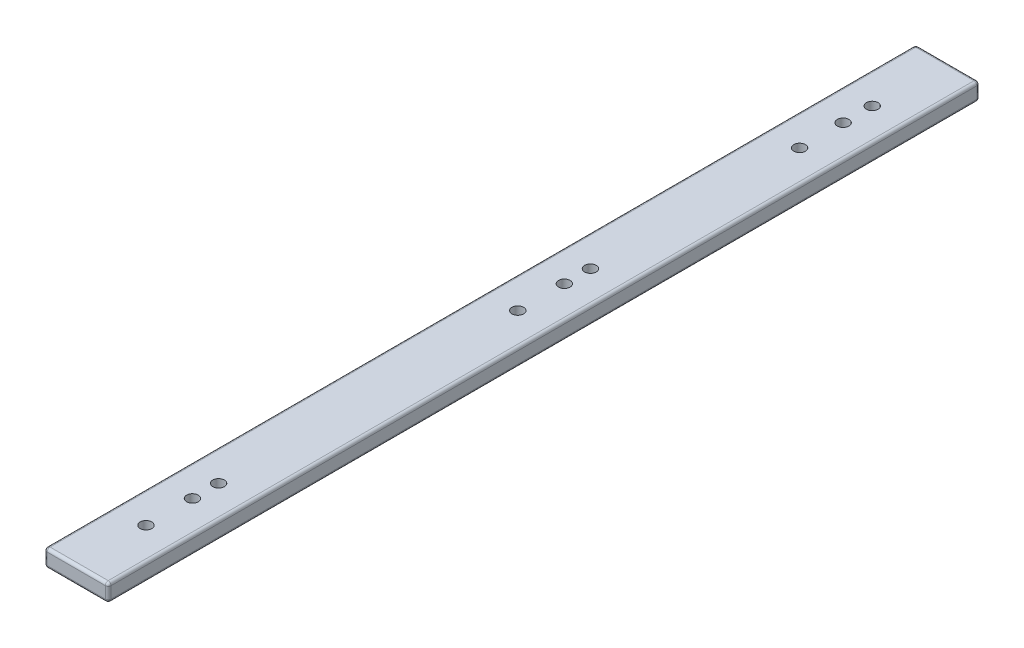
SolidWorks part; units mm, degrees
ref_plane "Front Plane" through (0, 0, 0) normal (0, 0, 1) x (1, 0, 0)
ref_plane "Top Plane" through (0, 0, 0) normal (0, 1, 0) x (1, 0, 0)
ref_plane "Right Plane" through (0, 0, 0) normal (1, 0, 0) x (0, 0, -1)
sketch "Sketch1" plane through (0, 0, 0) normal (0, 0, 1) x (1, 0, 0)
  line L1 (-11, -3) -> (11, -3)
  line L2 (-11, -3) -> (-11, 3)
  line L3 (-11, 3) -> (11, 3)
  line L4 (11, -3) -> (11, 3)
  line L5 (-11, -3) -> (11, 3) construction
  line L6 (-11, 3) -> (11, -3) construction
  point P0 (0, 0)
  dimension "D1" = 22
  dimension "D2" = 6
extrude "Boss-Extrude1" add sketch "Sketch1" along normal blind 300
sketch "Sketch3" plane through (0, 3, 0) normal (0, 1, 0) x (1, 0, 0)
  line L0 (11, -300) -> (11, 0) construction
  line L1 (11, 0) -> (-11, 0) construction
  line L2 (11, -300) -> (-11, -300) construction
  circle A0 centre (0, -26) radius 2
  circle A1 centre (0, -36) radius 2
  circle A2 centre (0, -51) radius 2
  circle A3 centre (0, -260) radius 2
  circle A4 centre (0, -276) radius 2
  circle A5 centre (0, -251) radius 2
  circle A6 centre (0, -148) radius 2
  circle A7 centre (0, -123) radius 2
  circle A8 centre (0, -132) radius 2
  dimension "D1" = 4
  dimension "D2" = 4
  dimension "D3" = 4
  dimension "D4" = 4
  dimension "D5" = 4
  dimension "D11" = 4
  dimension "D12" = 4
  dimension "D13" = 4
  dimension "D14" = 4
  dimension "D6" = 26
  dimension "D7" = 36
  dimension "D8" = 51
  dimension "D9" = 16
  dimension "D10" = 24
  dimension "D15" = 49
  dimension "D16" = 11
  dimension "D17" = 103
  dimension "D18" = 119
  dimension "D19" = 128
extrude "Cut-Extrude1" cut sketch "Sketch3" against normal blind 6
fillet "Fillet1" radius 1 12 edges at (0, -3, 300) (-11, 0, 300) (0, 3, 300) (11, 0, 300) (0, 3, 0) (-11, 0, 0) (0, -3, 0) (11, 0, 0) (-11, 3, 150) (-11, -3, 150) (11, -3, 150) (11, 3, 150)
